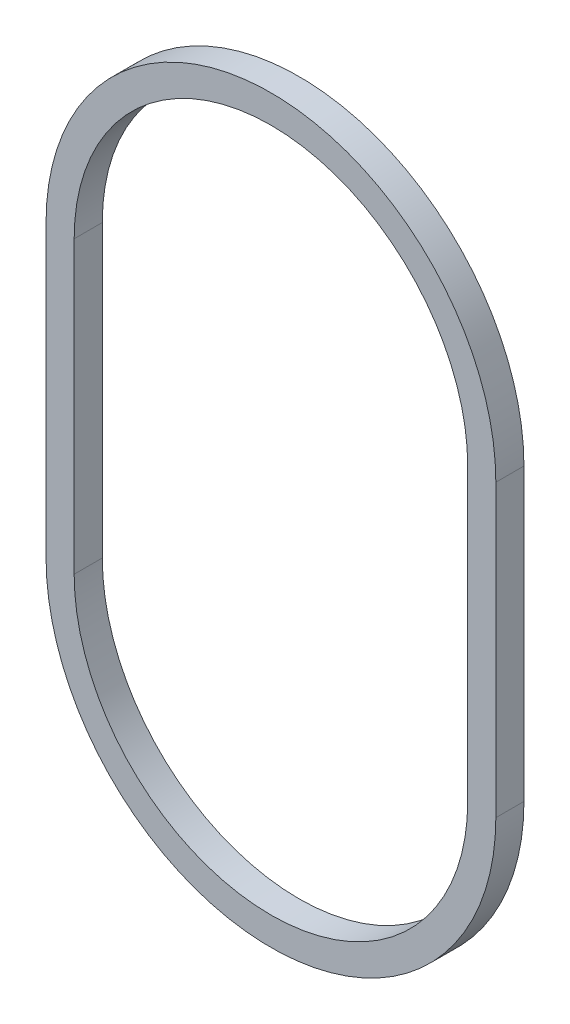
SolidWorks part; units mm, degrees
ref_plane "Front Plane" through (0, 0, 0) normal (0, 0, 1) x (1, 0, 0)
ref_plane "Top Plane" through (0, 0, 0) normal (0, 1, 0) x (1, 0, 0)
ref_plane "Right Plane" through (0, 0, 0) normal (1, 0, 0) x (0, 0, -1)
sketch "Sketch1" plane through (0, 0, 0) normal (0, 0, 1) x (1, 0, 0)
  line L0 (-24, -31) -> (-24, 0)
  line L1 (24, -31) -> (24, 0)
  line L2 (-21, -31) -> (-21, 0)
  line L3 (21, -31) -> (21, 0)
  arc A0 (24, 0) -> (-24, 0) centre (0, 0) ccw
  arc A1 (-24, -31) -> (24, -31) centre (0, -31) ccw
  arc A2 (21, 0) -> (-21, 0) centre (0, 0) ccw
  arc A3 (-21, -31) -> (21, -31) centre (0, -31) ccw
  dimension "D1" = 48
  dimension "D2" = 48
  dimension "D3" = 31
  dimension "D4" = 3
extrude "Boss-Extrude1" add sketch "Sketch1" along normal mid plane 3
